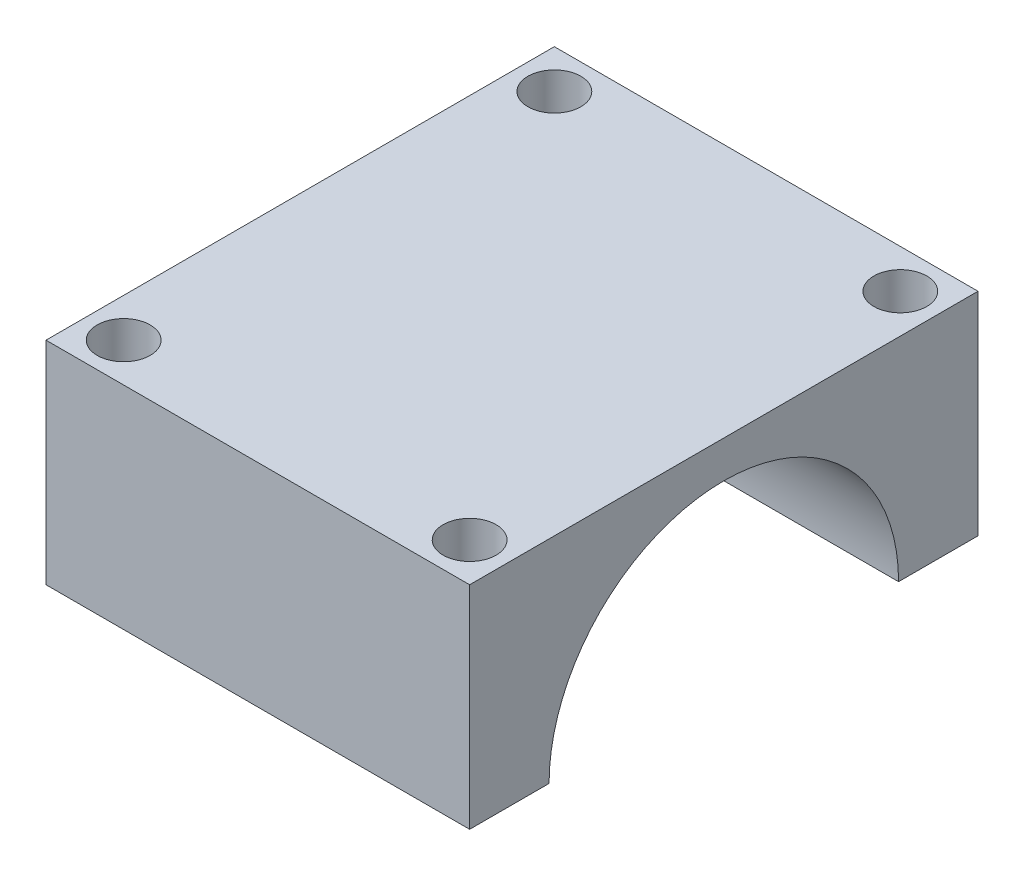
SolidWorks part; units mm, degrees
ref_plane "Front Plane" through (0, 0, 0) normal (0, 0, 1) x (1, 0, 0)
ref_plane "Top Plane" through (0, 0, 0) normal (0, 1, 0) x (1, 0, 0)
ref_plane "Right Plane" through (0, 0, 0) normal (1, 0, 0) x (0, 0, -1)
sketch "Sketch1" plane through (0, 0, 0) normal (0, 1, 0) x (1, 0, 0)
  line L1 (-15, -18) -> (15, -18)
  line L2 (-15, -18) -> (-15, 18)
  line L3 (-15, 18) -> (15, 18)
  line L4 (15, -18) -> (15, 18)
  line L5 (-15, -18) -> (15, 18) construction
  line L6 (-15, 18) -> (15, -18) construction
  point P0 (0, 0)
  dimension "D1" = 30
  dimension "D2" = 36
extrude "Boss-Extrude1" add sketch "Sketch1" along normal blind 30
sketch "Sketch3" plane through (15, 0, 0) normal (1, 0, 0) x (0, 0, -1)
  line L0 (0, 0) -> (0, 30) construction
  line L1 (-18, 0) -> (18, 0) construction
  line L2 (-18, 30) -> (18, 30) construction
  circle A0 centre (0, 15) radius 12.375
  dimension "D1" = 24.75
extrude "Cut-Extrude1" cut sketch "Sketch3" against normal blind 40
sketch "Sketch5" plane through (0, 30, 0) normal (0, 1, 0) x (1, 0, 0)
  line L7 (15, 18) -> (-15, 18) construction
  line L9 (-15, 18) -> (-15, -18) construction
  line L10 (0, 0) -> (0, 2.7791) construction
  line L11 (0, 2.7791) -> (0, 0) construction
  line L12 (0, 0) -> (-2.7536, 0) construction
  circle A1 centre (-12.25, 15.25) radius 1.875
  circle A2 centre (-12.25, -15.25) radius 1.875
  circle A3 centre (12.25, -15.25) radius 1.875
  circle A4 centre (12.25, 15.25) radius 1.875
  point P0 (0, 0)
  dimension "D2" = 3.75
  dimension "D3" = 2.75
  dimension "D4" = 2.75
extrude "Cut-Extrude2" cut sketch "Sketch5" against normal blind 40
sketch "Sketch7" plane through (0, 0, 0) normal (1, 0, 0) x (0, 0, -1)
  line L0 (-18, 30) -> (-18, 0) construction
  line L1 (-18, 15) -> (18, 15)
  line L2 (-18, 15) -> (-18, 0)
  line L3 (-18, 0) -> (18, 0)
  line L4 (18, 15) -> (18, 0)
extrude "Cut-Extrude3" cut sketch "Sketch7" against normal through all from surface at 15 starting at face at (15, 15, -12.375)
